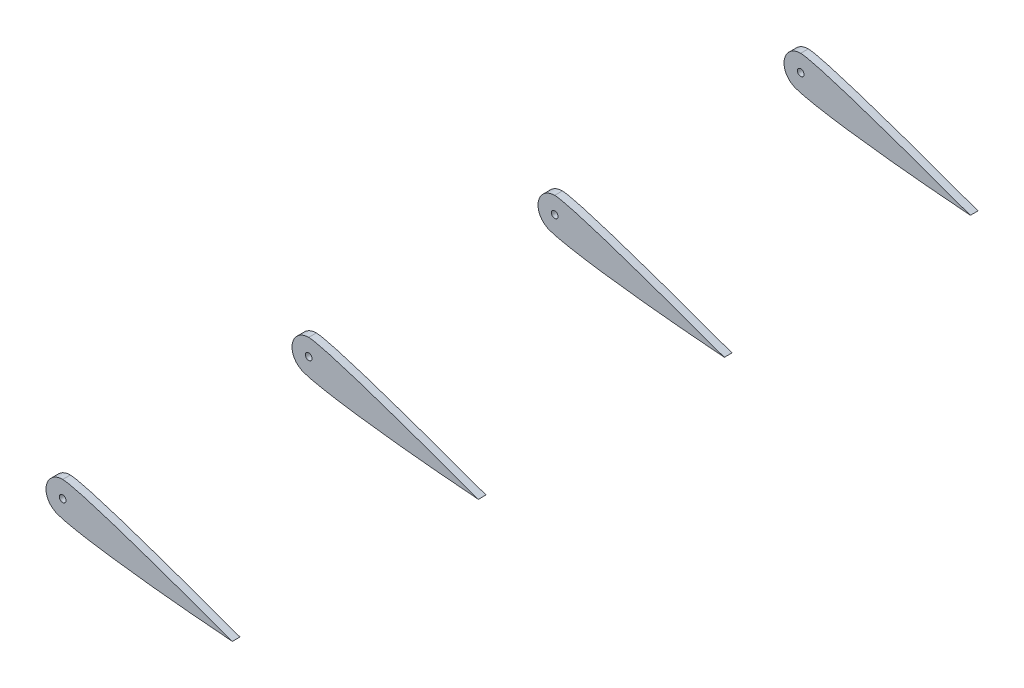
SolidWorks part; units mm, degrees
material "Balsa"
ref_plane "Front Plane" through (0, 0, 0) normal (0, 0, 1) x (1, 0, 0)
ref_plane "Top Plane" through (0, 0, 0) normal (0, 1, 0) x (1, 0, 0)
ref_plane "Right Plane" through (0, 0, 0) normal (1, 0, 0) x (0, 0, -1)
sketch "Sketch2" plane through (0, 0, 0) normal (0, 0, 1) x (1, 0, 0)
  arc A0 (0, 5) -> (-2.4254, -4.3723) centre (0, 0) ccw
  circle A1 centre (0, 0) radius 1
  spline S0 degree 2 poles (0, 5) (5.8325, 4.8504) (50.8, -11.6107) knots 0 0 0 1 1 1
  spline S1 degree 3 poles (-2.4254, -4.3723) (-0.7538, -5.8111) (16.9221, -8.9624) (50.8, -11.6107) knots 0 0 0 0 1 1 1 1
extrude "Boss-Extrude4" add sketch "Sketch2" along normal blind 2.286
ref_plane "Plane6" through (0, 0, 73.66) normal (0, 0, 1) x (1, 0, 0)
ref_plane "Plane7" through (0, 0, 147.32) normal (0, 0, 1) x (1, 0, 0)
ref_plane "Plane8" through (0, 0, 220.98) normal (0, 0, 1) x (1, 0, 0)
sketch "Sketch9" plane through (0, 0, 73.66) normal (0, 0, 1) x (1, 0, 0)
  arc A0 (0, 5) -> (-2.4254, -4.3723) centre (0, 0) ccw
  circle A1 centre (0, 0) radius 1
  spline S0 degree 2 poles (0, 5) (5.8325, 4.8504) (50.8, -11.6107) knots 0 0 0 1 1 1
  spline S1 degree 3 poles (-2.4254, -4.3723) (-0.7538, -5.8111) (16.9221, -8.9624) (50.8, -11.6107) knots 0 0 0 0 1 1 1 1
extrude "Boss-Extrude5" add sketch "Sketch9" along normal blind 2.286 separate body
sketch "Sketch10" plane through (0, 0, 147.32) normal (0, 0, 1) x (1, 0, 0)
  arc A0 (0, 5) -> (-2.4254, -4.3723) centre (0, 0) ccw
  circle A1 centre (0, 0) radius 1
  spline S0 degree 2 poles (0, 5) (5.8325, 4.8504) (50.8, -11.6107) knots 0 0 0 1 1 1
  spline S1 degree 3 poles (-2.4254, -4.3723) (-0.7538, -5.8111) (16.9221, -8.9624) (50.8, -11.6107) knots 0 0 0 0 1 1 1 1
extrude "Boss-Extrude6" add sketch "Sketch10" along normal blind 2.286 separate body
sketch "Sketch13" plane through (0, 0, 220.98) normal (0, 0, 1) x (1, 0, 0)
  arc A0 (0, 5) -> (-2.4254, -4.3723) centre (0, 0) ccw
  circle A1 centre (0, 0) radius 1
  spline S0 degree 2 poles (0, 5) (5.8325, 4.8504) (50.8, -11.6107) knots 0 0 0 1 1 1
  spline S1 degree 3 poles (-2.4254, -4.3723) (-0.7538, -5.8111) (16.9221, -8.9624) (50.8, -11.6107) knots 0 0 0 0 1 1 1 1
extrude "Boss-Extrude7" add sketch "Sketch13" along normal blind 2.286 separate body
